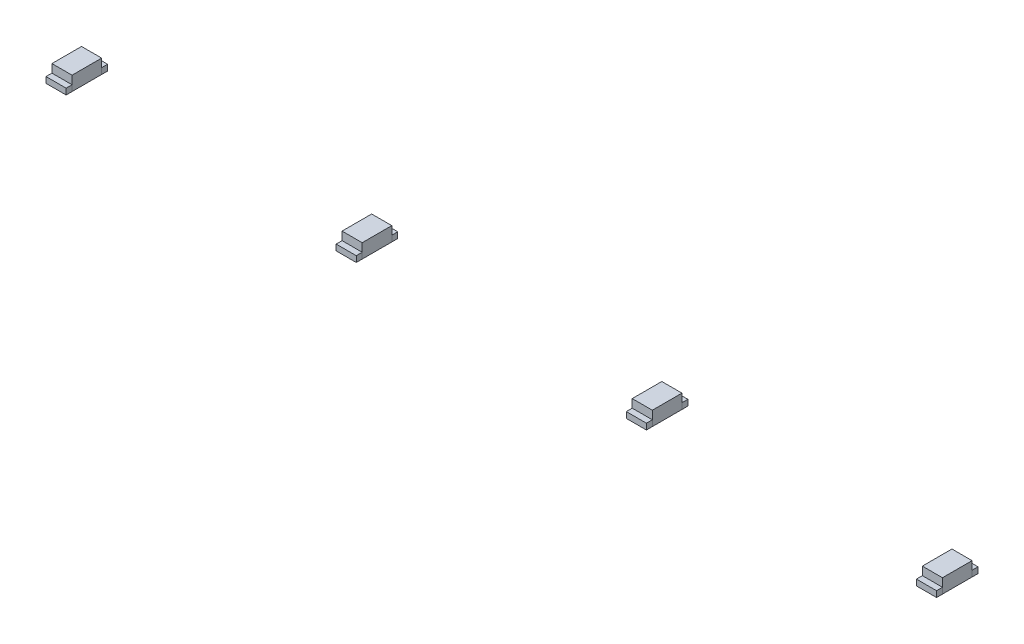
SolidWorks part; units mm, degrees
ref_plane "Front" through (0, 0, 0) normal (0, 0, 1) x (1, 0, 0)
ref_plane "Top" through (0, 0, 0) normal (0, 1, 0) x (1, 0, 0)
ref_plane "Right" through (0, 0, 0) normal (1, 0, 0) x (0, 0, -1)
sketch "Sketch1" plane through (0, 0, 0) normal (0, 1, 0) x (1, 0, 0)
  line L0 (0, 3.5488) -> (0, 0) construction
  line L1 (-18.8, 0.625) -> (-17.95, 0.625)
  line L2 (-18.8, 0.625) -> (-18.8, -0.625)
  line L3 (-18.8, -0.625) -> (-17.95, -0.625)
  line L4 (-17.95, 0.625) -> (-17.95, -0.625)
  line L5 (0, 0) -> (3.4283, 0) construction
  line L6 (17.95, 0.625) -> (17.95, -0.625)
  line L7 (18.8, -0.625) -> (17.95, -0.625)
  line L8 (18.8, 0.625) -> (18.8, -0.625)
  line L9 (18.8, 0.625) -> (17.95, 0.625)
  line L10 (-6.55, 0.625) -> (-5.7, 0.625)
  line L11 (-6.55, 0.625) -> (-6.55, -0.625)
  line L12 (-6.55, -0.625) -> (-5.7, -0.625)
  line L13 (-5.7, 0.625) -> (-5.7, -0.625)
  line L18 (5.7, 0.625) -> (5.7, -0.625)
  line L19 (6.55, -0.625) -> (5.7, -0.625)
  line L20 (6.55, 0.625) -> (6.55, -0.625)
  line L21 (6.55, 0.625) -> (5.7, 0.625)
  line L22 (-17.95, 0.625) -> (-6.55, 0.625) construction
  line L24 (-5.7, 0.625) -> (5.7, 0.625) construction
  line L25 (6.55, 0.625) -> (17.95, 0.625) construction
  point P8 (-17.95, 0)
  dimension "D1" = 1.25
  dimension "D2" = 0.85
  dimension "D3" = 12.25
extrude "Boss-Extrude1" add sketch "Sketch1" along normal blind 0.6
sketch "Sketch2" plane through (0, 0, 0) normal (0, 1, 0) x (1, 0, 0)
  line L0 (-6.55, 0.625) -> (-6.55, -0.625) construction
  line L1 (-18.8, 0.875) -> (-17.95, 0.875)
  line L2 (-18.8, 0.875) -> (-18.8, 0.625)
  line L3 (-18.8, 0.625) -> (-17.95, 0.625)
  line L4 (-17.95, 0.875) -> (-17.95, 0.625)
  line L5 (-6.55, 0.875) -> (-5.7, 0.875)
  line L6 (-6.55, 0.875) -> (-6.55, 0.625)
  line L7 (-6.55, 0.625) -> (-5.7, 0.625)
  line L8 (-5.7, 0.875) -> (-5.7, 0.625)
  line L13 (-18.8, 0.625) -> (-18.8, -0.625) construction
  line L15 (0, 3.4735) -> (0, 0) construction
  line L16 (0, 3.5488) -> (0, 0) construction
  line L17 (0, 0) -> (3.3183, 0) construction
  line L18 (0, 0) -> (3.4283, 0) construction
  line L19 (5.7, 0.875) -> (5.7, 0.625)
  line L20 (6.55, 0.625) -> (5.7, 0.625)
  line L21 (6.55, 0.875) -> (6.55, 0.625)
  line L22 (6.55, 0.875) -> (5.7, 0.875)
  line L23 (17.95, 0.875) -> (17.95, 0.625)
  line L24 (18.8, 0.625) -> (17.95, 0.625)
  line L25 (18.8, 0.875) -> (18.8, 0.625)
  line L26 (18.8, 0.875) -> (17.95, 0.875)
  line L27 (18.8, -0.875) -> (17.95, -0.875)
  line L28 (18.8, -0.875) -> (18.8, -0.625)
  line L29 (18.8, -0.625) -> (17.95, -0.625)
  line L30 (17.95, -0.875) -> (17.95, -0.625)
  line L31 (6.55, -0.875) -> (5.7, -0.875)
  line L32 (6.55, -0.875) -> (6.55, -0.625)
  line L33 (6.55, -0.625) -> (5.7, -0.625)
  line L34 (5.7, -0.875) -> (5.7, -0.625)
  line L39 (-5.7, -0.875) -> (-5.7, -0.625)
  line L40 (-6.55, -0.625) -> (-5.7, -0.625)
  line L41 (-6.55, -0.875) -> (-6.55, -0.625)
  line L42 (-6.55, -0.875) -> (-5.7, -0.875)
  line L43 (-17.95, -0.875) -> (-17.95, -0.625)
  line L44 (-18.8, -0.625) -> (-17.95, -0.625)
  line L45 (-18.8, -0.875) -> (-18.8, -0.625)
  line L46 (-18.8, -0.875) -> (-17.95, -0.875)
  dimension "D1" = 1.75
extrude "Boss-Extrude2" add sketch "Sketch2" along normal blind 0.25
sketch "Sketch3" plane through (-18.8, 0, 0) normal (-1, 0, 0) x (0, 0, 1)
  line L0 (0.625, 0.25) -> (0.625, 0)
  line L1 (-0.875, 0) -> (0.875, 0) construction
  line L2 (-0.625, 0.25) -> (-0.625, 0)
split line "Split Line1"
